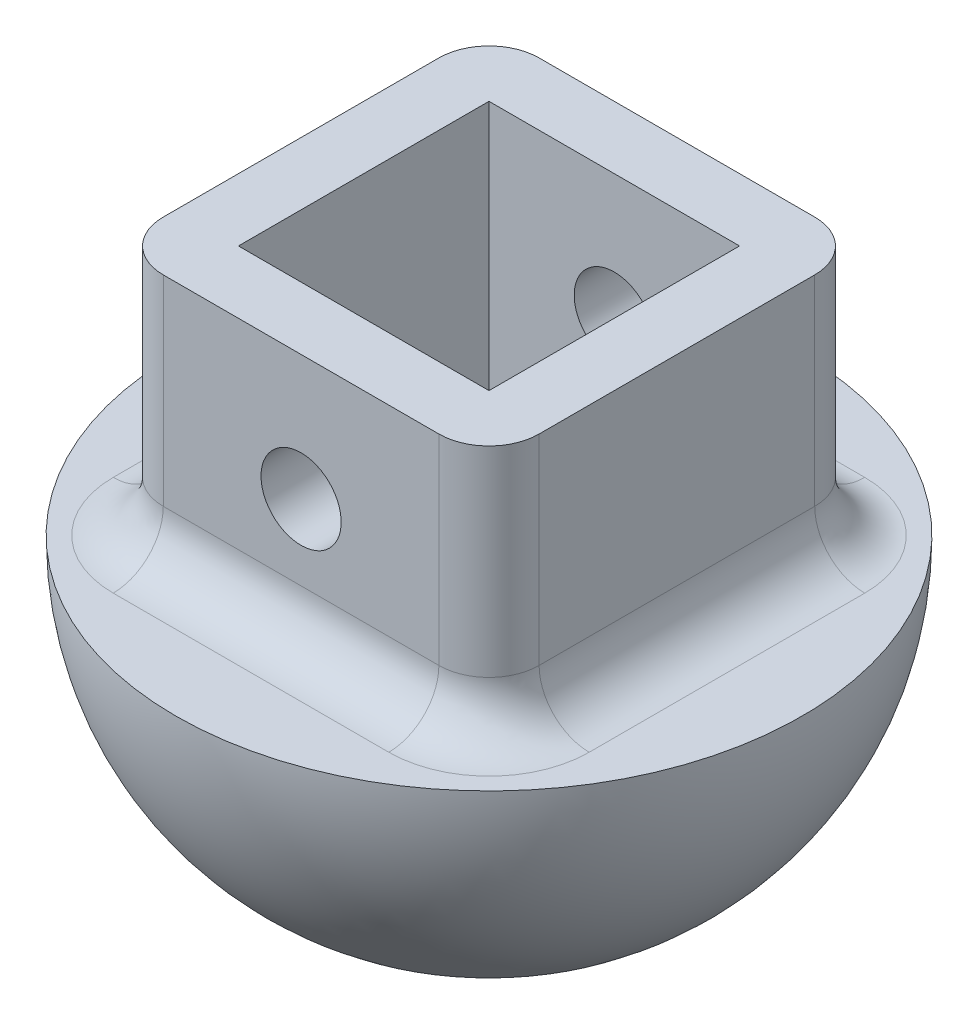
SolidWorks part; units mm, degrees
ref_plane "Front Plane" through (0, 0, 0) normal (0, 0, 1) x (1, 0, 0)
ref_plane "Top Plane" through (0, 0, 0) normal (0, 1, 0) x (1, 0, 0)
ref_plane "Right Plane" through (0, 0, 0) normal (1, 0, 0) x (0, 0, -1)
sketch "Sketch4" plane through (0, 0, 0) normal (0, 1, 0) x (1, 0, 0)
  line L0 (-12.5, 0) -> (12.5, 0)
  arc A0 (-12.5, 0) -> (12.5, 0) centre (0, 0) ccw
  point P8 (0, 0)
  dimension "D1" = 25
revolve "Revolve2" add sketch "Sketch4" angle 180 about L0
sketch "Sketch1" plane through (0, 0, 0) normal (0, 1, 0) x (1, 0, 0)
  line L1 (-5, 5) -> (5, 5)
  line L2 (-5, 5) -> (-5, -5)
  line L3 (-5, -5) -> (5, -5)
  line L4 (5, 5) -> (5, -5)
  line L5 (-5, 5) -> (5, -5) construction
  line L6 (-5, -5) -> (5, 5) construction
  line L7 (-7.5, 7.5) -> (7.5, 7.5)
  line L8 (-7.5, 7.5) -> (-7.5, -7.5)
  line L9 (-7.5, -7.5) -> (7.5, -7.5)
  line L10 (7.5, 7.5) -> (7.5, -7.5)
  line L11 (-7.5, 7.5) -> (7.5, -7.5) construction
  line L12 (-7.5, -7.5) -> (7.5, 7.5) construction
  point P0 (0, 0)
  point P6 (0, 0)
  dimension "D1" = 10
  dimension "D2" = 15
extrude "Boss-Extrude1" add sketch "Sketch1" along normal blind 10
sketch "Sketch2" plane through (0, 0, 5) normal (0, 0, -1) x (-1, 0, 0)
  line L0 (0, 0) -> (0, 10) construction
  line L1 (-7.5, 10) -> (7.5, 10) construction
  circle A0 centre (0, 5) radius 1.6
  dimension "D1" = 3.2
extrude "Cut-Extrude1" cut sketch "Sketch2" against normal blind 10 and the other way blind 20
fillet "Fillet1" radius 2 8 edges at (-7.5, 5, 7.5) (-7.5, 5, -7.5) (7.5, 5, -7.5) (7.5, 5, 7.5) (0, 0, -7.5) (7.5, 0, 0) (-7.5, 0, 0) (0, 0, 7.5)
